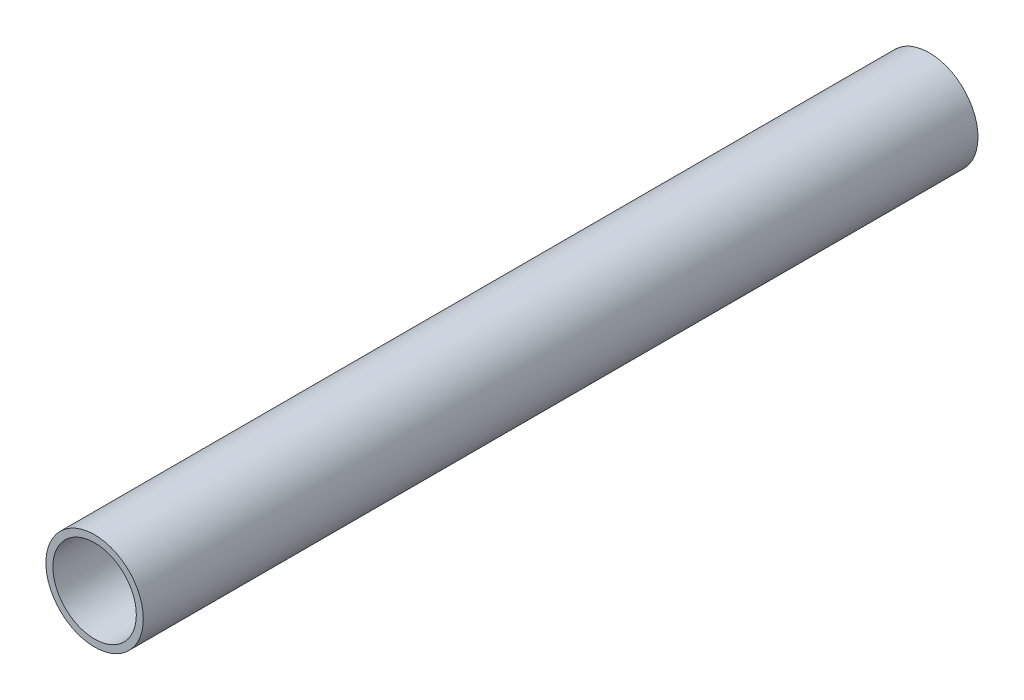
SolidWorks part; units mm, degrees
material "Thornel VCB-20 Carbon Cloth"
ref_plane "Front Plane" through (0, 0, 0) normal (0, 0, 1) x (1, 0, 0)
ref_plane "Top Plane" through (0, 0, 0) normal (0, 1, 0) x (1, 0, 0)
ref_plane "Right Plane" through (0, 0, 0) normal (1, 0, 0) x (0, 0, -1)
sketch "Sketch1" plane through (0, 0, 0) normal (0, 0, 1) x (1, 0, 0)
  circle A0 centre (0, 0) radius 9.525
  circle A1 centre (0, 0) radius 11.1125
  dimension "D1" = 19.05
  dimension "D2" = 22.225
extrude "Boss-Extrude1" add sketch "Sketch1" along normal mid plane 190.5
scale "Scale1" scale about centroid uniform scaling yes scale factor 0.35
